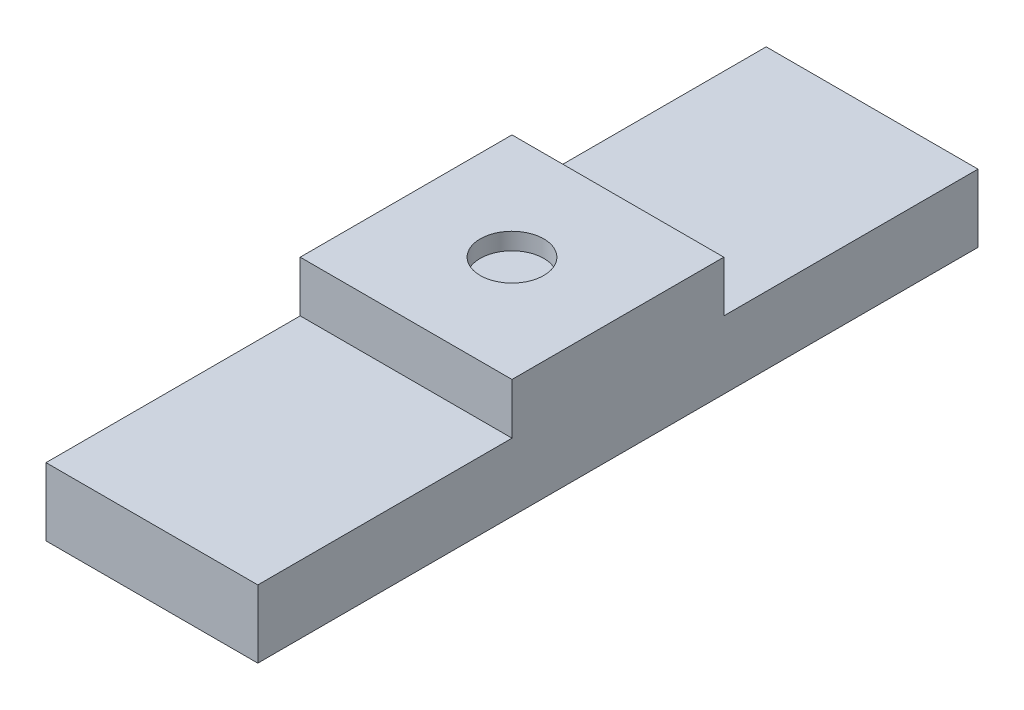
SolidWorks part; units mm, degrees
ref_plane "Front Plane" through (0, 0, 0) normal (0, 0, 1) x (1, 0, 0)
ref_plane "Top Plane" through (0, 0, 0) normal (0, 1, 0) x (1, 0, 0)
ref_plane "Right Plane" through (0, 0, 0) normal (1, 0, 0) x (0, 0, -1)
sketch "Sketch1" plane through (0, 0, 0) normal (0, 1, 0) x (1, 0, 0)
  line L1 (0, 0) -> (2.5, 0)
  line L2 (0, 0) -> (0, 8.5)
  line L3 (0, 8.5) -> (2.5, 8.5)
  line L4 (2.5, 0) -> (2.5, 8.5)
  dimension "D1" = 8.5
  dimension "D2" = 2.5
extrude "Boss-Extrude1" add sketch "Sketch1" along normal blind 0.8
sketch "Sketch2" plane through (0, 0.8, 0) normal (0, 1, 0) x (1, 0, 0)
  line L0 (1.25, 8.5) -> (1.25, 0) construction
  line L1 (2.5, 8.5) -> (0, 8.5) construction
  line L2 (0, 0) -> (2.5, 0) construction
  line L3 (0, 4.25) -> (2.5, 4.25) construction
  line L4 (0, 8.5) -> (0, 0) construction
  line L5 (2.5, 0) -> (2.5, 8.5) construction
  line L7 (2.5, 3) -> (0, 3)
  line L8 (2.5, 3) -> (2.5, 5.5)
  line L9 (2.5, 5.5) -> (0, 5.5)
  line L10 (0, 3) -> (0, 5.5)
  line L11 (2.5, 3) -> (0, 5.5) construction
  line L12 (2.5, 5.5) -> (0, 3) construction
  point P12 (1.25, 4.25)
  dimension "D1" = 2.5
extrude "Boss-Extrude2" add sketch "Sketch2" along normal blind 0.6
sketch "Sketch3" plane through (0, 1.4, 0) normal (0, 1, 0) x (1, 0, 0)
  line L0 (1.25, 5.5) -> (1.25, 3) construction
  line L1 (2.5, 5.5) -> (0, 5.5) construction
  line L2 (0, 3) -> (2.5, 3) construction
  circle A0 centre (1.25, 4.25) radius 0.375
  dimension "D1" = 0.75
extrude "Cut-Extrude1" cut sketch "Sketch3" against normal blind 0.2
